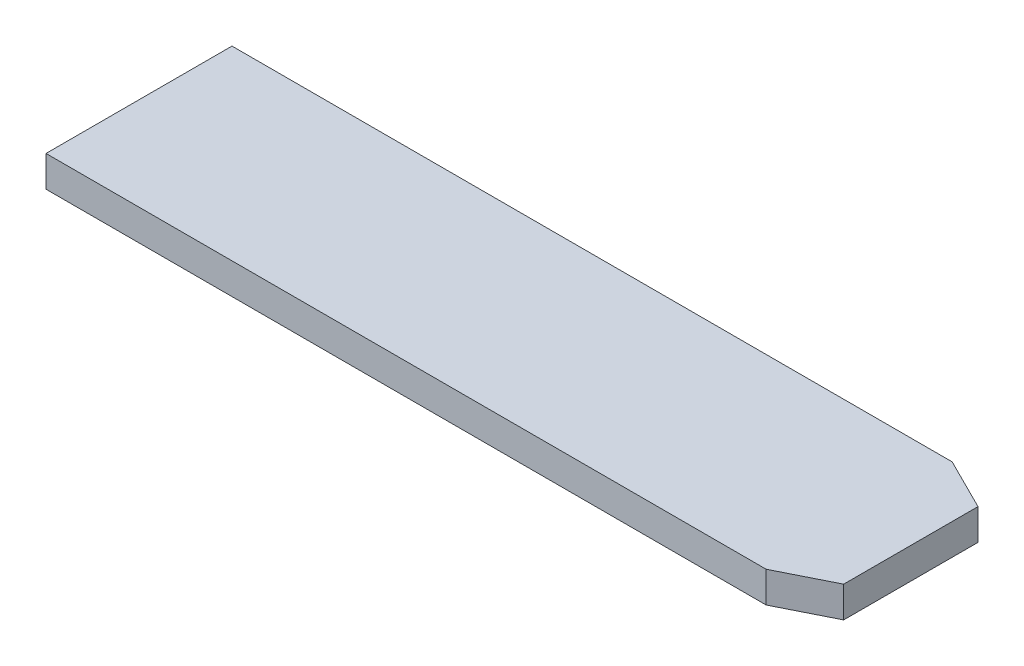
SolidWorks part; units mm, degrees
ref_plane "Front Plane" through (0, 0, 0) normal (0, 0, 1) x (1, 0, 0)
ref_plane "Top Plane" through (0, 0, 0) normal (0, 1, 0) x (1, 0, 0)
ref_plane "Right Plane" through (0, 0, 0) normal (1, 0, 0) x (0, 0, -1)
sketch "Sketch1" plane through (0, 0, 0) normal (0, 1, 0) x (1, 0, 0)
  line L1 (34.85, 9) -> (-34.85, 9)
  line L2 (34.85, 9) -> (34.85, -9)
  line L3 (34.85, -9) -> (-34.85, -9)
  line L4 (-34.85, 9) -> (-34.85, -9)
  line L5 (34.85, 9) -> (-34.85, -9) construction
  line L6 (34.85, -9) -> (-34.85, 9) construction
  point P0 (0, 0)
  dimension "D1" = 18
  dimension "D2" = 69.7
extrude "Boss-Extrude1" add sketch "Sketch1" along normal blind 3
ref_plane "Plane1" through (39.85, 0, 0) normal (1, 0, 0) x (0, 0, -1)
sketch "Sketch3" plane through (39.85, 0, 0) normal (1, 0, 0) x (0, 0, -1)
  line L0 (0, 0) -> (0, 3) construction
  line L3 (-9, 3) -> (9, 3) construction
  line L4 (-9, 0) -> (9, 0) construction
  line L5 (-6.5, 3) -> (6.5, 3)
  line L6 (-6.5, 3) -> (-6.5, 0)
  line L7 (-6.5, 0) -> (6.5, 0)
  line L8 (6.5, 3) -> (6.5, 0)
  line L9 (-6.5, 3) -> (6.5, 0) construction
  line L10 (-6.5, 0) -> (6.5, 3) construction
  point P4 (0, 1.5)
  dimension "D1" = 13
loft "Loft1" add profiles "Sketch3" section "Sketch3" section face at (34.85, 1.5, 0)
